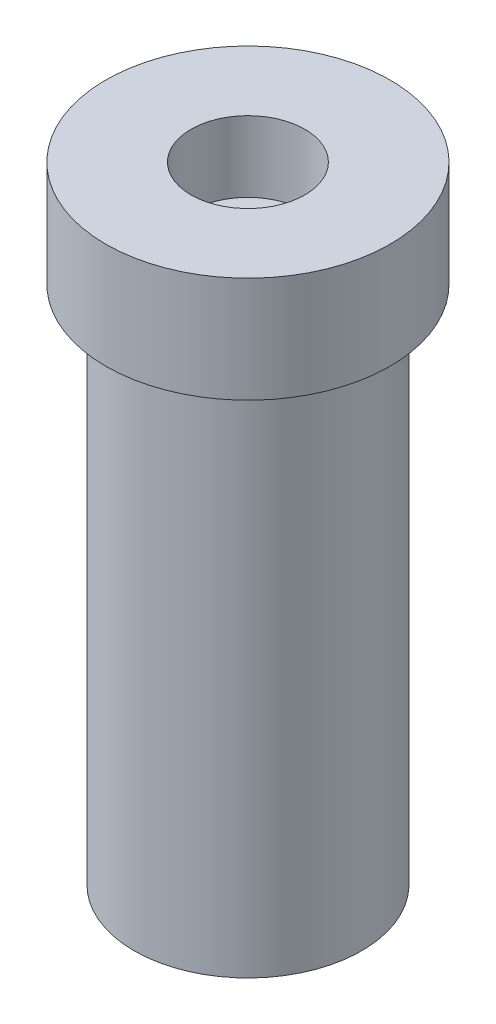
SolidWorks part; units mm, degrees
ref_plane "Front Plane" through (0, 0, 0) normal (0, 0, 1) x (1, 0, 0)
ref_plane "Top Plane" through (0, 0, 0) normal (0, 1, 0) x (1, 0, 0)
ref_plane "Right Plane" through (0, 0, 0) normal (1, 0, 0) x (0, 0, -1)
sketch "Sketch1" plane through (0, 0, 0) normal (0, 0, 1) x (1, 0, 0)
  line L0 (0, 11.5409) -> (0, -6.9538) construction
  line L1 (0, 0) -> (1.75, 0)
  line L2 (1.75, 0) -> (1.75, 8)
  line L3 (1.75, 8) -> (2.1859, 8)
  line L4 (2.1859, 8) -> (2.1859, 9.6246)
  line L5 (2.1859, 9.6246) -> (0.875, 9.6246)
  line L6 (0.875, 9.6246) -> (0.875, 8.5364)
  line L7 (0.875, 8.5364) -> (0, 8.5364)
  line L8 (0, 8.5364) -> (0, 0)
  dimension "D1" = 3.5
  dimension "D2" = 8
revolve "Revolve1" add sketch "Sketch1" angle 360 about L0
